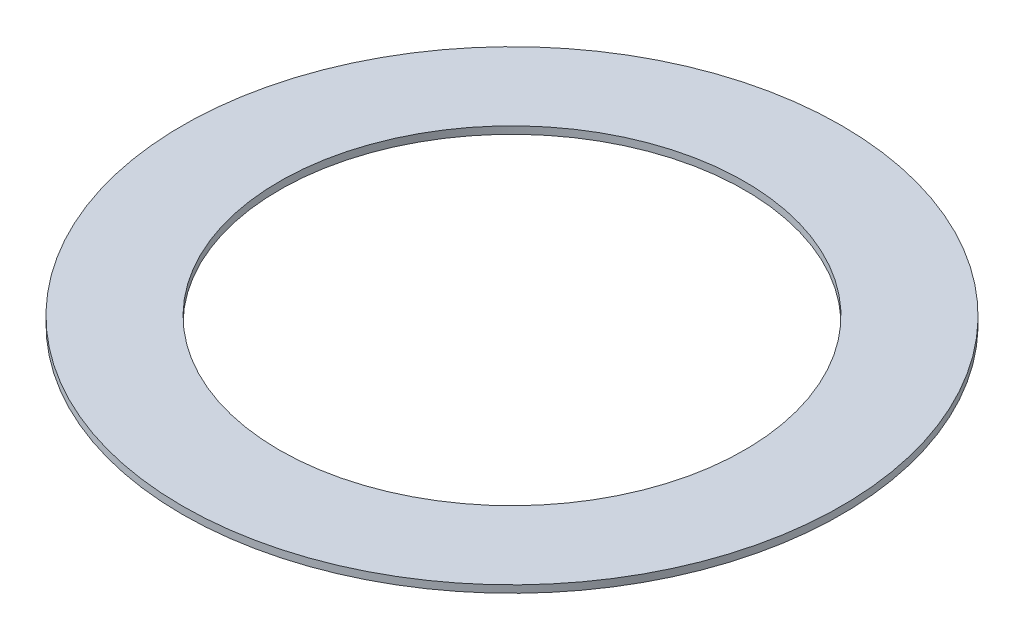
SolidWorks part; units mm, degrees
material "Oak"
ref_plane "Front Plane" through (0, 0, 0) normal (0, 0, 1) x (1, 0, 0)
ref_plane "Top Plane" through (0, 0, 0) normal (0, 1, 0) x (1, 0, 0)
ref_plane "Right Plane" through (0, 0, 0) normal (1, 0, 0) x (0, 0, -1)
sketch "Sketch1" plane through (0, 0, 0) normal (0, 1, 0) x (1, 0, 0)
  circle A0 centre (0, 0) radius 76.2
  circle A1 centre (0, 0) radius 107.95
  dimension "D1" = 152.4
  dimension "D2" = 215.9
extrude "Boss-Extrude1" add sketch "Sketch1" along normal blind 2.4
